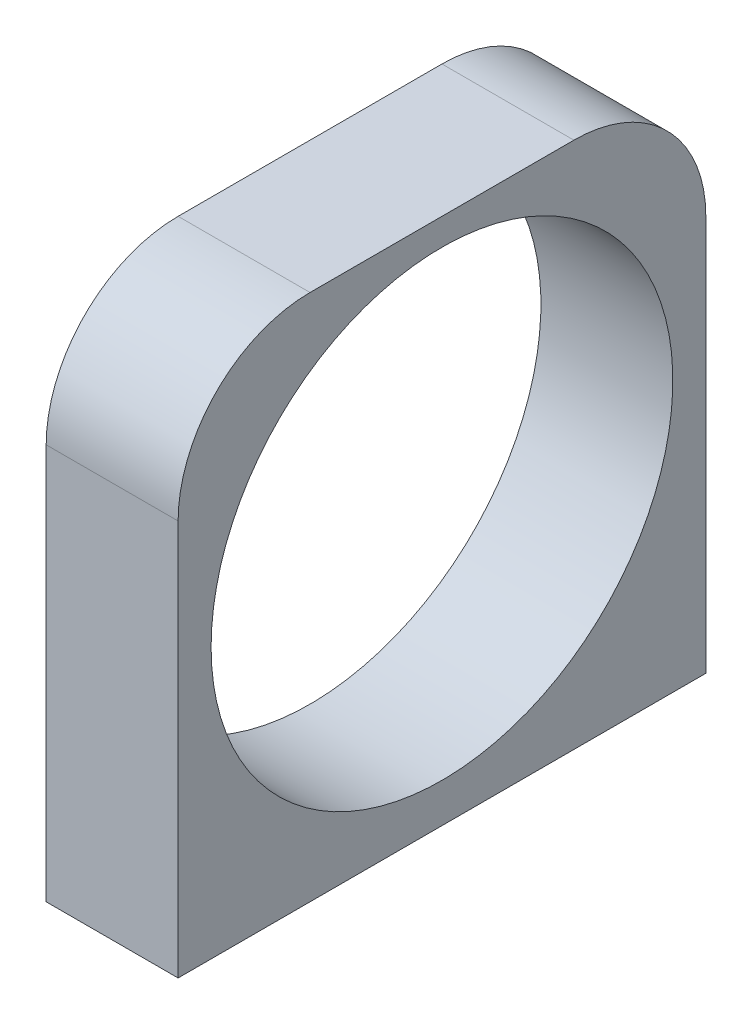
SolidWorks part; units mm, degrees
ref_plane "Front Plane" through (0, 0, 0) normal (0, 0, 1) x (1, 0, 0)
ref_plane "Top Plane" through (0, 0, 0) normal (0, 1, 0) x (1, 0, 0)
ref_plane "Right Plane" through (0, 0, 0) normal (1, 0, 0) x (0, 0, -1)
sketch "Sketch1" plane through (0, 0, 0) normal (0, 1, 0) x (1, 0, 0)
  line L1 (-3.175, -12.7) -> (3.175, -12.7)
  line L2 (-3.175, -12.7) -> (-3.175, 12.7)
  line L3 (-3.175, 12.7) -> (3.175, 12.7)
  line L4 (3.175, -12.7) -> (3.175, 12.7)
  line L5 (-3.175, -12.7) -> (3.175, 12.7) construction
  line L6 (-3.175, 12.7) -> (3.175, -12.7) construction
  point P0 (0, 0)
  dimension "D1" = 6.35
  dimension "D2" = 25.4
extrude "Boss-Extrude1" add sketch "Sketch1" along normal blind 25.4
fillet "Fillet1" radius 6.35 2 edges at (0, 25.4, -12.7) (0, 25.4, 12.7)
sketch "Sketch2" plane through (-3.175, 0, 0) normal (-1, 0, 0) x (0, 0, 1)
  line L0 (-12.7, 0) -> (12.7, 0) construction
  circle A0 centre (0, 13) radius 11.1125
  dimension "D1" = 22.225
  dimension "D2" = 13
extrude "Cut-Extrude1" cut sketch "Sketch2" against normal through all
